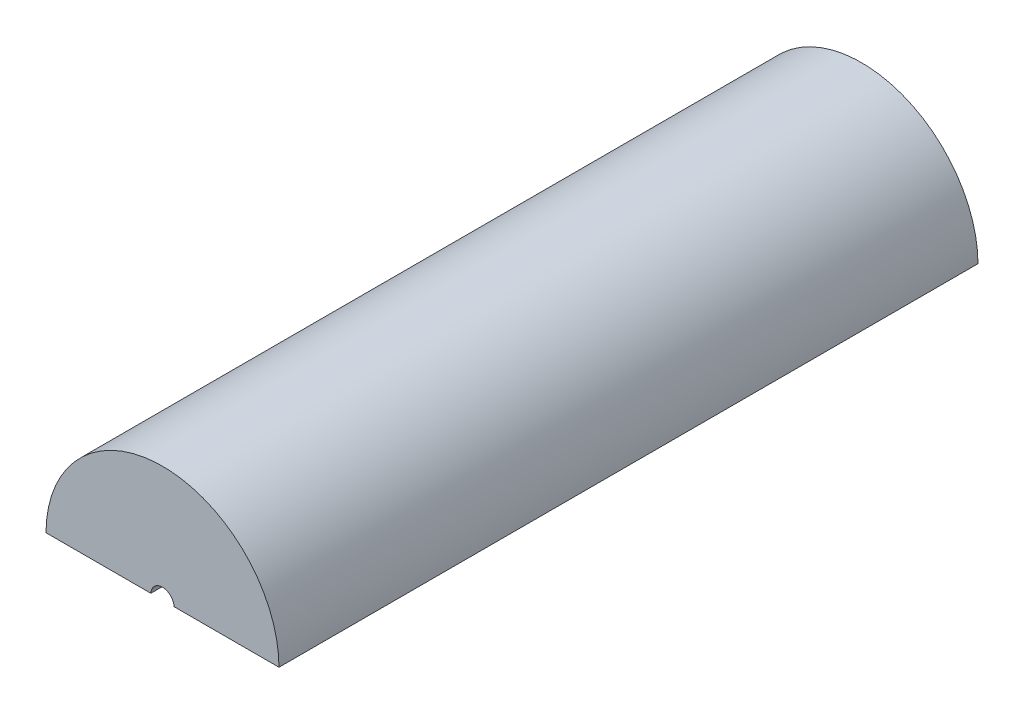
SolidWorks part; units mm, degrees
ref_plane "Plan de face" through (0, 0, 0) normal (0, 0, 1) x (1, 0, 0)
ref_plane "Plan de dessus" through (0, 0, 0) normal (0, 1, 0) x (1, 0, 0)
ref_plane "Plan de droite" through (0, 0, 0) normal (1, 0, 0) x (0, 0, -1)
sketch "Esquisse1" plane through (0, 0, 0) normal (0, 0, 1) x (1, 0, 0)
  circle A0 centre (0, 0) radius 20
extrude "Boss.-Extru.1" add sketch "Esquisse1" against normal blind 120
ref_plane "Plan1" through (0, 0, -5) normal (0, 0, 1) x (1, 0, 0)
sketch "Esquisse3" plane through (0, 0, -5) normal (0, 0, 1) x (1, 0, 0)
  circle A0 centre (0, 0) radius 16
extrude "Enlèv. mat.-Extru.1" cut sketch "Esquisse3" against normal blind 90
ref_plane "Plan3" through (0, 0, 0) normal (0, 1, 0) x (1, 0, 0)
sketch "Esquisse6" plane through (0, 0, -120) normal (0, 0, -1) x (-1, 0, 0)
  line L0 (-21.4279, 0) -> (-21.4279, -0.1)
  line L1 (21.9997, 0) -> (-21.9997, 0) construction
  line L2 (-21.4279, -0.1) -> (22.2825, -0.1)
  line L3 (22.2825, -0.1) -> (22.2825, 0.1)
  line L4 (22.2825, 0.1) -> (-21.4279, 0.1)
  line L5 (-21.4279, 0.1) -> (-21.4279, 0)
extrude "Enlèv. mat.-Extru.3" cut sketch "Esquisse6" against normal blind 140
sketch "Esquisse8" plane through (0, 0.1, 0) normal (0, -1, 0) x (1, 0, 0)
  line L0 (-15.9997, -95) -> (15.9997, -95)
  line L1 (15.9997, -95) -> (-15.9997, -95) construction
  arc A0 (-15.9997, -95) -> (15.9997, -95) centre (0, -95) cw
revolve "Enlèvement de matière-Révolution3" cut sketch "Esquisse8" angle 360 about L0
sketch "Esquisse9" plane through (0, 0, 0) normal (0, 0, 1) x (1, 0, 0)
  circle A0 centre (0, 0) radius 2
extrude "Enlèv. mat.-Extru.4" cut sketch "Esquisse9" against normal blind 10
